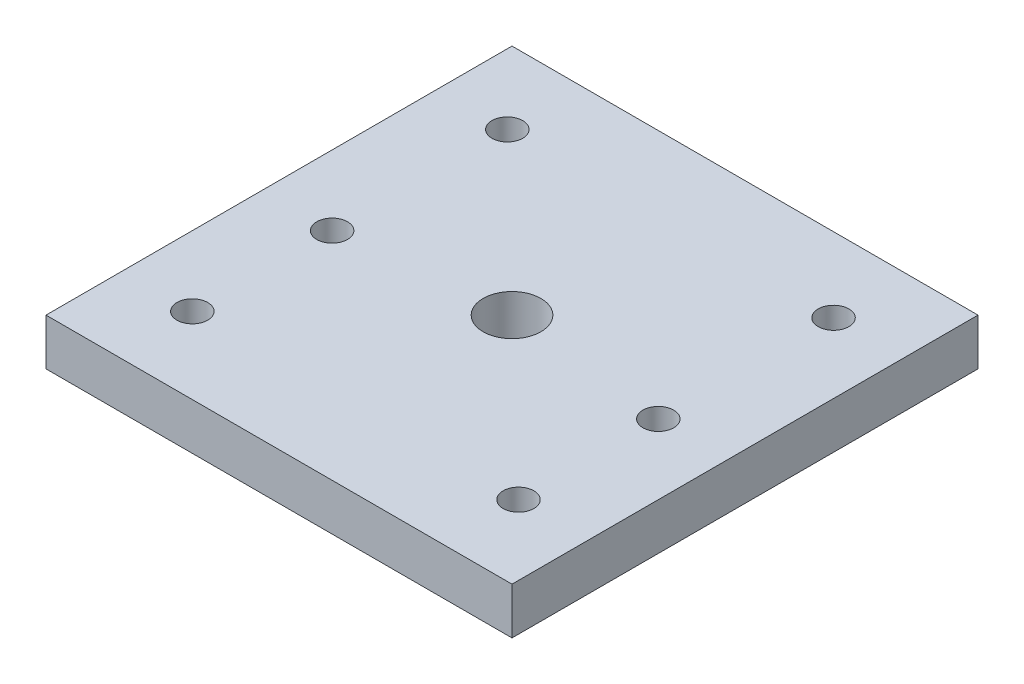
SolidWorks part; units mm, degrees
ref_plane "Front Plane" through (0, 0, 0) normal (0, 0, 1) x (1, 0, 0)
ref_plane "Top Plane" through (0, 0, 0) normal (0, 1, 0) x (1, 0, 0)
ref_plane "Right Plane" through (0, 0, 0) normal (1, 0, 0) x (0, 0, -1)
sketch "Sketch2" plane through (0, 0, 0) normal (0, 1, 0) x (1, 0, 0)
  line L1 (63.5, -63.5) -> (-63.5, -63.5)
  line L2 (63.5, -63.5) -> (63.5, 63.5)
  line L3 (63.5, 63.5) -> (-63.5, 63.5)
  line L4 (-63.5, -63.5) -> (-63.5, 63.5)
  line L5 (63.5, -63.5) -> (-63.5, 63.5) construction
  line L6 (63.5, 63.5) -> (-63.5, -63.5) construction
  point P0 (0, 0)
  dimension "D1" = 127
  dimension "D2" = 127
extrude "Boss-Extrude1" add sketch "Sketch2" along normal blind 12.7
hole_wizard "Ø10.0mm Dowel Hole1" positions "Sketch8" profile "Sketch9" hole size "Ø10.0" standard "ANSI Metric" end condition through all
sketch "Sketch8" plane through (0, 0, 0) normal (0, -1, 0) x (-1, 0, 0)
  line L0 (-63.5, 63.5) -> (63.5, 63.5) construction
  line L1 (-44.45, -63.5) -> (-44.45, 63.5) construction
  line L2 (63.5, -63.5) -> (-63.5, -63.5) construction
  line L3 (44.45, -63.5) -> (44.45, 63.5) construction
  point P0 (-44.45, 43.18)
  point P2 (-44.45, -4.572)
  point P4 (-44.45, -42.672)
  point P6 (44.45, 43.18)
  point P8 (44.45, -4.572)
  point P10 (44.45, -42.672)
  dimension "D1" = 47.752
  dimension "D2" = 38.1
  dimension "D3" = 20.32
  dimension "D4" = 47.752
  dimension "D5" = 20.32
  dimension "D6" = 38.1
  dimension "D7" = 19.05
  dimension "D8" = 19.05
sketch "Sketch9" plane through (44.45, 0, -43.18) normal (1, 0, 0) x (0, 0, -1)
  line L0 (0, 0) -> (0, 12.7)
  line L1 (0, 12.7) -> (4.191, 12.7)
  line L2 (4.191, 12.7) -> (4.191, 0)
  line L5 (4.191, 0) -> (0, 0)
  line L11 (0, -6.35) -> (0, 107.95) construction
  dimension "Thru Hole Dia." = 8.382
  dimension "Thru Hole Depth" = 12.7
sketch "Sketch12" plane through (0, 0, 0) normal (0, -1, 0) x (1, 0, 0)
  circle A0 centre (0, 0) radius 7.874
extrude "Cut-Extrude2" cut sketch "Sketch12" against normal through all
equation "\"D2@Sketch2\"=\"D1@Sketch2\""
equation "\"D4@Sketch8\"=\"D1@Sketch8\""
equation "\"D5@Sketch8\"=\"D3@Sketch8\""
equation "\"D6@Sketch8\"=\"D2@Sketch8\""
